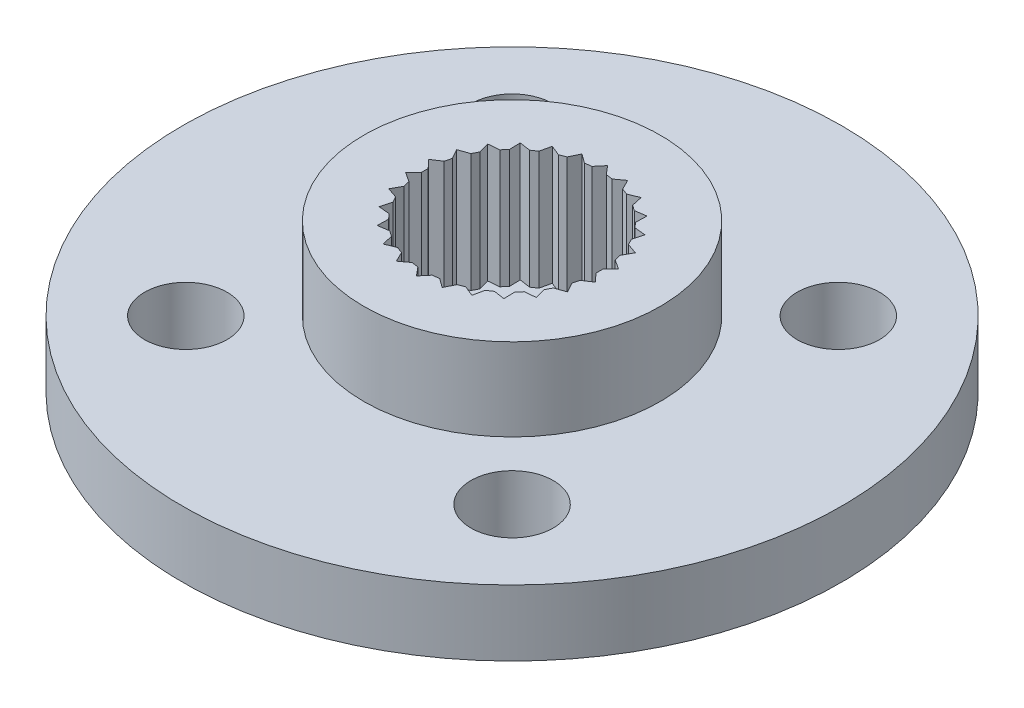
SolidWorks part; units mm, degrees
ref_plane "Спереди" through (0, 0, 0) normal (0, 0, 1) x (1, 0, 0)
ref_plane "Сверху" through (0, 0, 0) normal (0, 1, 0) x (1, 0, 0)
ref_plane "Справа" through (0, 0, 0) normal (1, 0, 0) x (0, 0, -1)
sketch "Эскиз1" plane through (0, 0, 0) normal (0, 0, 1) x (1, 0, 0)
  line L0 (10, 2) -> (0, 2)
  line L1 (0, 2) -> (0, 0)
  line L2 (0, 0) -> (10, 0)
  line L3 (10, 0) -> (10, 2)
  line L4 (0, 2) -> (0, 0) construction
revolve "Повернуть1" add sketch "Эскиз1" angle 360 about L4
sketch "Эскиз2" plane through (0, 2, 0) normal (0, 1, 0) x (-1, 0, 0)
  circle A0 centre (0, 0) radius 4.5
extrude "Бобышка-Вытянуть1" add sketch "Эскиз2" along normal blind 2.5
sketch "Эскиз3" plane through (0, 4.5, 0) normal (0, 1, 0) x (-1, 0, 0)
  line L0 (-2.7115, 1.0284) -> (-2.4779, 0.6107)
  line L1 (-2.4779, 0.6107) -> (-2.8789, 0.3496)
  line L2 (-2.8789, 0.3496) -> (-2.552, 0)
  line L3 (-2.552, 0) -> (-2.8789, -0.3496)
  line L4 (-2.8789, -0.3496) -> (-2.4779, -0.6107)
  line L5 (-2.4779, -0.6107) -> (-2.7115, -1.0284)
  line L6 (-2.7115, -1.0284) -> (-2.2597, -1.186)
  line L7 (-2.2597, -1.186) -> (-2.3867, -1.6474)
  line L8 (-2.3867, -1.6474) -> (-1.9102, -1.6923)
  line L9 (-1.9102, -1.6923) -> (-1.9231, -2.1707)
  line L10 (-1.9231, -2.1707) -> (-1.4497, -2.1003)
  line L11 (-1.4497, -2.1003) -> (-1.3477, -2.5678)
  line L12 (-1.3477, -2.5678) -> (-0.905, -2.3862)
  line L13 (-0.905, -2.3862) -> (-0.694, -2.8157)
  line L14 (-0.694, -2.8157) -> (-0.3076, -2.5334)
  line L15 (-0.3076, -2.5334) -> (0, -2.9)
  line L16 (0, -2.9) -> (0.3076, -2.5334)
  line L17 (0.3076, -2.5334) -> (0.694, -2.8157)
  line L18 (0.694, -2.8157) -> (0.905, -2.3862)
  line L19 (0.905, -2.3862) -> (1.3477, -2.5678)
  line L20 (1.3477, -2.5678) -> (1.4497, -2.1003)
  line L21 (1.4497, -2.1003) -> (1.9231, -2.1707)
  line L22 (1.9231, -2.1707) -> (1.9102, -1.6923)
  line L23 (1.9102, -1.6923) -> (2.3867, -1.6474)
  line L24 (2.3867, -1.6474) -> (2.2597, -1.186)
  line L25 (2.2597, -1.186) -> (2.7115, -1.0284)
  line L26 (2.7115, -1.0284) -> (2.4779, -0.6107)
  line L27 (2.4779, -0.6107) -> (2.8789, -0.3496)
  line L28 (2.8789, -0.3496) -> (2.552, 0)
  line L29 (2.552, 0) -> (2.8789, 0.3496)
  line L30 (2.8789, 0.3496) -> (2.4779, 0.6107)
  line L31 (2.4779, 0.6107) -> (2.7115, 1.0284)
  line L32 (2.7115, 1.0284) -> (2.2597, 1.186)
  line L33 (2.2597, 1.186) -> (2.3867, 1.6474)
  line L34 (2.3867, 1.6474) -> (1.9102, 1.6923)
  line L35 (1.9102, 1.6923) -> (1.9231, 2.1707)
  line L36 (1.9231, 2.1707) -> (1.4497, 2.1003)
  line L37 (1.4497, 2.1003) -> (1.3477, 2.5678)
  line L38 (1.3477, 2.5678) -> (0.905, 2.3862)
  line L39 (0.905, 2.3862) -> (0.694, 2.8157)
  line L40 (0.694, 2.8157) -> (0.3076, 2.5334)
  line L41 (0.3076, 2.5334) -> (0, 2.9)
  line L42 (0, 2.9) -> (-0.3076, 2.5334)
  line L43 (-0.3076, 2.5334) -> (-0.694, 2.8157)
  line L44 (-0.694, 2.8157) -> (-0.905, 2.3862)
  line L45 (-0.905, 2.3862) -> (-1.3477, 2.5678)
  line L46 (-1.3477, 2.5678) -> (-1.4497, 2.1003)
  line L47 (-1.4497, 2.1003) -> (-1.9231, 2.1707)
  line L48 (-1.9231, 2.1707) -> (-1.9102, 1.6923)
  line L49 (-1.9102, 1.6923) -> (-2.3867, 1.6474)
  line L50 (-2.3867, 1.6474) -> (-2.2597, 1.186)
  line L51 (-2.2597, 1.186) -> (-2.7115, 1.0284)
extrude "Вырез-Вытянуть1" cut sketch "Эскиз3" against normal blind 3.6
hole_wizard "Диаметр отверстия Ø3.0 (3)1" positions "Эскиз5" profile "Эскиз4" hole size "Ø3.0" standard "Ansi Metric"
sketch "Эскиз5" plane through (0, 0.9, 0) normal (0, 1, 0) x (1, 0, 0)
  point P0 (0, 0)
sketch "Эскиз4" plane through (0, 0.9, 0) normal (1, 0, 0) x (0, 0, 1)
  line L0 (0, 0) -> (0, 0.9)
  line L1 (0, 0.9) -> (1.5, 0.9)
  line L2 (1.5, 0.9) -> (1.5, 0)
  line L5 (1.5, 0) -> (0, 0)
  line L11 (0, -6.35) -> (0, 107.95) construction
  dimension "Диаметр сквозного отверстия" = 3
  dimension "Глубина сквозного отверстия" = 0.9
hole_wizard "Диаметр отверстия Ø2.5 (2.5)1" positions "Эскиз7" profile "Эскиз6" hole size "Ø2.5" standard "Ansi Metric"
sketch "Эскиз7" plane through (0, 2, 0) normal (0, 1, 0) x (1, 0, 0)
  point P0 (-4.9497, 4.9497)
  point P1 (4.9497, 4.9497)
  point P2 (4.9497, -4.9497)
  point P3 (-4.9497, -4.9497)
sketch "Эскиз6" plane through (-4.9497, 2, -4.9497) normal (1, 0, 0) x (0, 0, 1)
  line L0 (0, 0) -> (0, 2)
  line L1 (0, 2) -> (1.25, 2)
  line L2 (1.25, 2) -> (1.25, 0)
  line L5 (1.25, 0) -> (0, 0)
  line L11 (0, -6.35) -> (0, 107.95) construction
  dimension "Диаметр сквозного отверстия" = 2.5
  dimension "Глубина сквозного отверстия" = 2
chamfer "Фаска1" distance 0.1406 angle 43.077 26 edges at (-2.4779, 2.7, -0.6107) (-2.4779, 2.7, 0.6107) (-2.2597, 2.7, -1.186) (-2.2597, 2.7, 1.186) (2.552, 2.7, 0) (-1.9102, 2.7, -1.6923) (-1.9102, 2.7, 1.6923) (-1.4497, 2.7, -2.1003) (-1.4497, 2.7, 2.1003) (-0.905, 2.7, -2.3862) (-0.905, 2.7, 2.3862) (2.4779, 2.7, 0.6107) (-0.3076, 2.7, -2.5334) (0.3076, 2.7, -2.5334) (-0.3076, 2.7, 2.5334) (0.3076, 2.7, 2.5334) (0.905, 2.7, -2.3862) (0.905, 2.7, 2.3862) (1.4497, 2.7, -2.1003) (1.4497, 2.7, 2.1003) (1.9102, 2.7, -1.6923) (1.9102, 2.7, 1.6923) (2.2597, 2.7, -1.186) (2.2597, 2.7, 1.186) (2.4779, 2.7, -0.6107) (-2.552, 2.7, 0)
